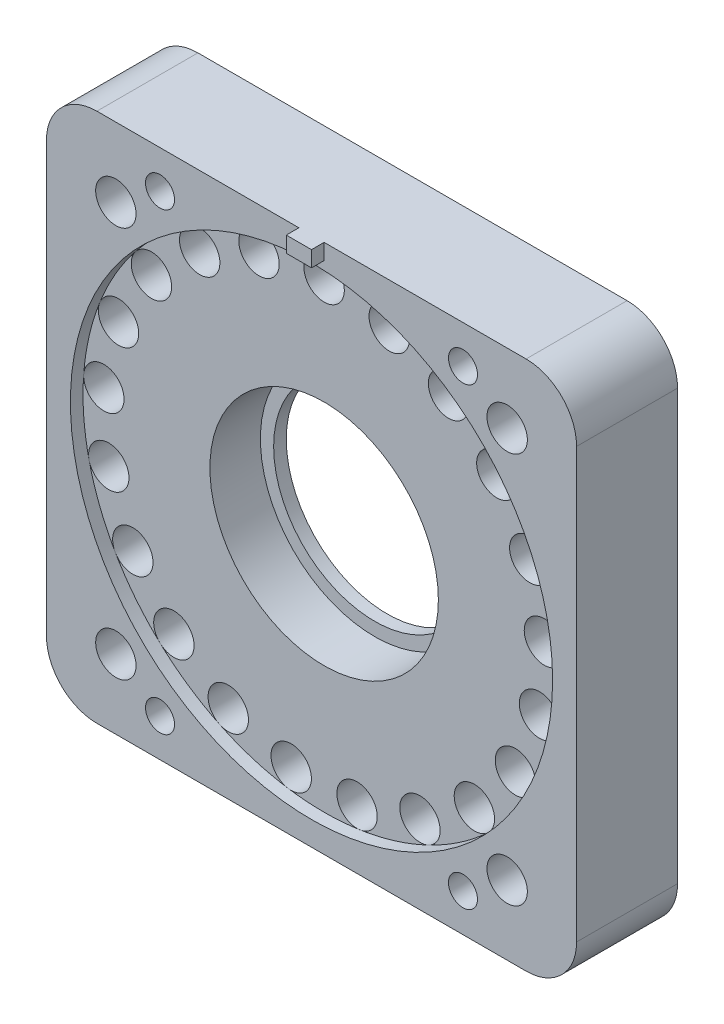
SolidWorks part; units mm, degrees
ref_plane "前视基准面" through (0, 0, 0) normal (0, 0, 1) x (1, 0, 0)
ref_plane "上视基准面" through (0, 0, 0) normal (0, 1, 0) x (1, 0, 0)
ref_plane "右视基准面" through (0, 0, 0) normal (1, 0, 0) x (0, 0, -1)
sketch "草图1" plane through (0, 0, 0) normal (0, 0, 1) x (1, 0, 0)
  line L1 (-21, 21) -> (21, 21)
  line L2 (-21, 21) -> (-21, -21)
  line L3 (-21, -21) -> (21, -21)
  line L4 (21, 21) -> (21, -21)
  line L5 (0, -21) -> (0, 21) construction
  line L6 (-21, 0) -> (21, 0) construction
  point P0 (0, 0)
  dimension "D1" = 42
  dimension "D2" = 42
extrude "凸台-拉伸1" add sketch "草图1" along normal blind 8
sketch "草图2" plane through (0, 0, 8) normal (0, 0, 1) x (1, 0, 0)
  circle A0 centre (0, 0) radius 19.1
  dimension "D1" = 38.2
extrude "切除-拉伸1" cut sketch "草图2" against normal blind 1
sketch "草图3" plane through (0, 0, 7) normal (0, 0, 1) x (1, 0, 0)
  line L0 (0, 17.5) -> (0, 0) construction
  circle A0 centre (0, 17.5) radius 1.6
  circle A1 centre (0, 0) radius 19.1 construction
  dimension "D1" = 3.2
extrude "切除-拉伸2" cut sketch "草图3" against normal blind 2.5
pattern_circular "阵列(圆周)1" count 21 over 360 about axis through (0, 0, 0) along (0, 0, 1) of "切除-拉伸2"
sketch "草图4" plane through (0, 0, 7) normal (0, 0, 1) x (1, 0, 0)
  circle A0 centre (0, 0) radius 9.05
  dimension "D1" = 18.1
extrude "切除-拉伸3" cut sketch "草图4" against normal blind 4
sketch "草图5" plane through (0, 0, 0) normal (0, 0, -1) x (-1, 0, 0)
  circle A0 centre (0, 0) radius 11.05
  dimension "D1" = 22.1
extrude "切除-拉伸4" cut sketch "草图5" against normal blind 2
sketch "草图6" plane through (0, 0, 2) normal (0, 0, -1) x (-1, 0, 0)
  circle A0 centre (0, 0) radius 8
  dimension "D1" = 16
extrude "切除-拉伸5" cut sketch "草图6" against normal through all
fillet "圆角1" radius 4 4 edges at (21, 21, 4) (21, -21, 4) (-21, -21, 4) (-21, 21, 4)
sketch "草图8" plane through (0, 0, 8) normal (0, 0, 1) x (1, 0, 0)
  line L0 (17, 21) -> (-17, 21) construction
  line L1 (-21, 17) -> (-21, -17) construction
  line L2 (0, 0) -> (-22.6859, 0) construction
  line L3 (0, 0) -> (0, 28.8454) construction
  circle A0 centre (-12, 18) radius 1.15
  circle A1 centre (-15.5, 15.5) radius 1.6
  circle A2 centre (15.5, 15.5) radius 1.6
  circle A3 centre (12, 18) radius 1.15
  circle A4 centre (15.5, -15.5) radius 1.6
  circle A5 centre (12, -18) radius 1.15
  circle A6 centre (-12, -18) radius 1.15
  circle A7 centre (-15.5, -15.5) radius 1.6
  dimension "D3" = 2.3
  dimension "D4" = 3.2
  dimension "D1" = 3
  dimension "D2" = 9
  dimension "D5" = 15.5
  dimension "D6" = 15.5
extrude "切除-拉伸6" cut sketch "草图8" against normal through all
sketch "草图9" plane through (0, 0, 0) normal (0, 0, -1) x (-1, 0, 0)
  circle A0 centre (-12, 18) radius 1.65
  circle A1 centre (12, 18) radius 1.65
  circle A2 centre (-12, -18) radius 1.65
  circle A3 centre (12, -18) radius 1.65
  dimension "D1" = 3.3
extrude "切除-拉伸7" cut sketch "草图9" against normal blind 6
sketch "草图10" plane through (0, 0, 8) normal (0, 0, 1) x (1, 0, 0)
  line L0 (0, 0) -> (0, 22.25) construction
  line L4 (17, 21) -> (-17, 21) construction
  line L6 (-1, 21) -> (-1, 19.75)
  line L7 (-1, 19.75) -> (1, 19.75)
  line L8 (1, 21) -> (1, 19.75)
  line L9 (0, 19.75) -> (0, 22.25) construction
  line L10 (-1, 21) -> (1, 21) construction
  line L11 (-1, 21) -> (1, 21)
  point P3 (0, 21)
  dimension "D1" = 1.25
extrude "凸台-拉伸2" add sketch "草图10" along normal blind 1
